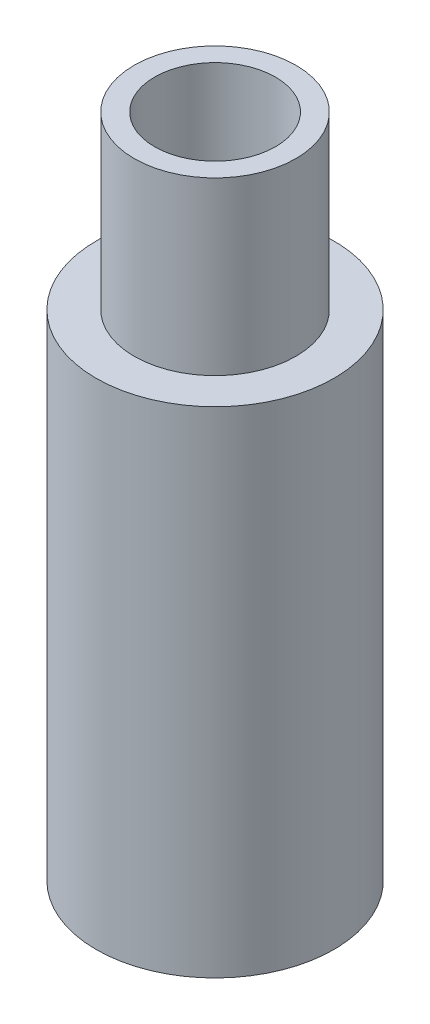
SolidWorks part; units mm, degrees
ref_plane "Front Plane" through (0, 0, 0) normal (0, 0, 1) x (1, 0, 0)
ref_plane "Top Plane" through (0, 0, 0) normal (0, 1, 0) x (1, 0, 0)
ref_plane "Right Plane" through (0, 0, 0) normal (1, 0, 0) x (0, 0, -1)
sketch "Sketch1" plane through (0, 0, 0) normal (0, 1, 0) x (1, 0, 0)
  circle A0 centre (0, 0) radius 3.175
  circle A1 centre (0, 0) radius 6.25
  dimension "D1" = 6.35
  dimension "D2" = 12.5
extrude "Boss-Extrude1" add sketch "Sketch1" along normal blind 35
sketch "Sketch2" plane through (0, 35, 0) normal (0, 1, 0) x (1, 0, 0)
  circle A0 centre (0, 0) radius 4.25
  dimension "D1" = 8.5
extrude "Cut-Extrude1" cut sketch "Sketch2" against normal blind 9 flip side to cut
sketch "Sketch3" plane through (0, 0, 0) normal (0, -1, 0) x (1, 0, 0)
  circle A1 centre (0, 0) radius 4.25
  dimension "D1" = 8.5
extrude "Cut-Extrude2" cut sketch "Sketch3" against normal blind 9
